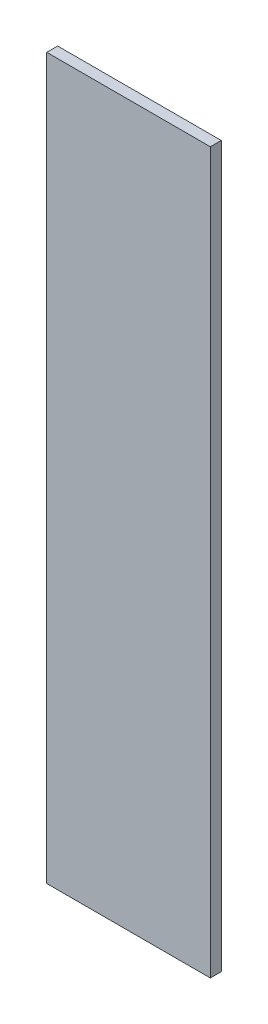
SolidWorks part; units mm, degrees
ref_plane "Front Plane" through (0, 0, 0) normal (0, 0, 1) x (1, 0, 0)
ref_plane "Top Plane" through (0, 0, 0) normal (0, 1, 0) x (1, 0, 0)
ref_plane "Right Plane" through (0, 0, 0) normal (1, 0, 0) x (0, 0, -1)
sketch "Sketch1" plane through (0, 0, 0) normal (0, 0, 1) x (1, 0, 0)
  line L1 (0, 0) -> (95.25, 0) construction
  line L2 (0, 0) -> (0, 431.8) construction
  line L3 (0, 431.8) -> (95.25, 431.8) construction
  line L4 (95.25, 0) -> (95.25, 431.8) construction
  line L5 (0, 431.8) -> (95.25, 431.8)
  line L6 (0, 431.8) -> (0, 12.7)
  line L7 (0, 12.7) -> (95.25, 12.7)
  line L8 (95.25, 431.8) -> (95.25, 12.7)
  dimension "D1" = 431.8
  dimension "D2" = 95.25
  dimension "D3" = 12.7
extrude "Boss-Extrude1" add sketch "Sketch1" along normal blind 6.35
